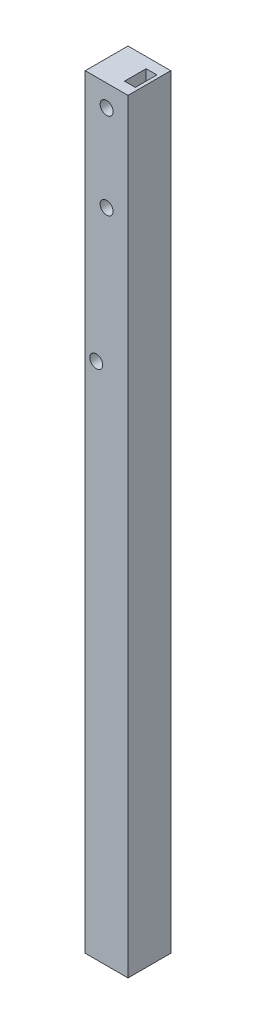
SolidWorks part; units mm, degrees
ref_plane "Спереди" through (0, 0, 0) normal (0, 0, 1) x (1, 0, 0)
ref_plane "Сверху" through (0, 0, 0) normal (0, 1, 0) x (1, 0, 0)
ref_plane "Справа" through (0, 0, 0) normal (1, 0, 0) x (0, 0, -1)
sketch "Эскиз1" plane through (0, 0, 0) normal (0, 1, 0) x (1, 0, 0)
  line L0 (2.2052, -5.0583) -> (2.2052, 4.8417) construction
  line L1 (4.2052, -5.0583) -> (-5.6948, -5.0583)
  line L2 (4.2052, -5.0583) -> (4.2052, 4.8417)
  line L3 (4.2052, 4.8417) -> (-5.6948, 4.8417)
  line L4 (-5.6948, -5.0583) -> (-5.6948, 4.8417)
  line L5 (-3.8948, -5.0583) -> (-3.8948, 4.8417) construction
  line L7 (0.9552, 2.3917) -> (3.4552, 2.3917)
  line L8 (0.9552, 2.3917) -> (0.9552, -2.6083)
  line L9 (0.9552, -2.6083) -> (3.4552, -2.6083)
  line L10 (3.4552, 2.3917) -> (3.4552, -2.6083)
  line L11 (0.9552, 2.3917) -> (3.4552, -2.6083) construction
  line L12 (0.9552, -2.6083) -> (3.4552, 2.3917) construction
  point P0 (0, 0)
  point P7 (0, 0)
  point P16 (2.2052, -0.1083)
  dimension "D6" = 5
  dimension "D7" = 2.5
  dimension "D2" = 9.9
  dimension "D8" = 2
  dimension "D9" = 1.8
extrude "Бобышка-Вытянуть1" add sketch "Эскиз1" along normal blind 177
sketch "Sketch2" plane through (0, 0, -4.8417) normal (0, 0, -1) x (-1, 0, 0)
  line L0 (0.7448, 177) -> (0.7448, 0) construction
  line L1 (-4.2052, 177) -> (5.6948, 177) construction
  line L2 (-4.2052, 0) -> (5.6948, 0) construction
  line L3 (3.1448, 0) -> (3.1448, 177) construction
  line L4 (-4.2052, 120) -> (4.6448, 120) construction
  line L5 (-4.2052, 177) -> (-4.2052, 0) construction
  circle A0 centre (0.7448, 172) radius 1.5
  circle A1 centre (3.1448, 120) radius 1.5
  circle A2 centre (0.7448, 152) radius 1.5
  dimension "D2" = 3
  dimension "D3" = 2.4
  dimension "D1" = 5
  dimension "D4" = 52
  dimension "D5" = 20
extrude "Cut-Extrude2" cut sketch "Sketch2" against normal through all
